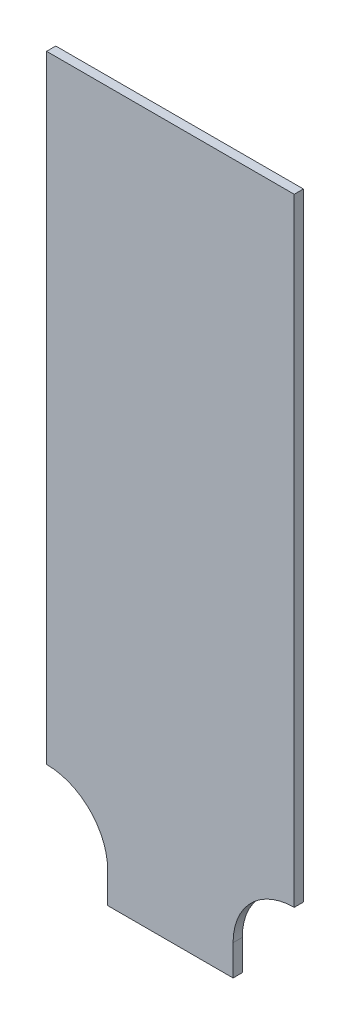
SolidWorks part; units mm, degrees
ref_plane "Face" through (0, 0, 0) normal (0, 0, 1) x (1, 0, 0)
ref_plane "Dessus" through (0, 0, 0) normal (0, 1, 0) x (1, 0, 0)
ref_plane "Droite" through (0, 0, 0) normal (1, 0, 0) x (0, 0, -1)
sketch "Esquisse1" plane through (0, 0, 0) normal (0, 0, 1) x (1, 0, 0)
  line L0 (0, 0) -> (0, 232) construction
  line L1 (40.5, 232) -> (-40.5, 232)
  line L2 (-40.5, 232) -> (-40.5, 30)
  line L3 (20.5, 0) -> (-20.5, 0)
  line L4 (-20.5, 0) -> (-20.5, 10)
  line L5 (-40.5, 30) -> (-40.5, 0) construction
  line L6 (40.5, 30) -> (40.5, 0) construction
  line L7 (20.5, 0) -> (20.5, 10)
  line L8 (40.5, 232) -> (40.5, 30)
  arc A0 (-40.5, 30) -> (-20.5, 10) centre (-40.5, 10) cw
  arc A1 (40.5, 30) -> (20.5, 10) centre (40.5, 10) ccw
  dimension "D3" = 20
  dimension "D1" = 232
  dimension "D2" = 40.5
  dimension "D4" = 30
extrude "Extrusion1" add sketch "Esquisse1" along normal blind 3
